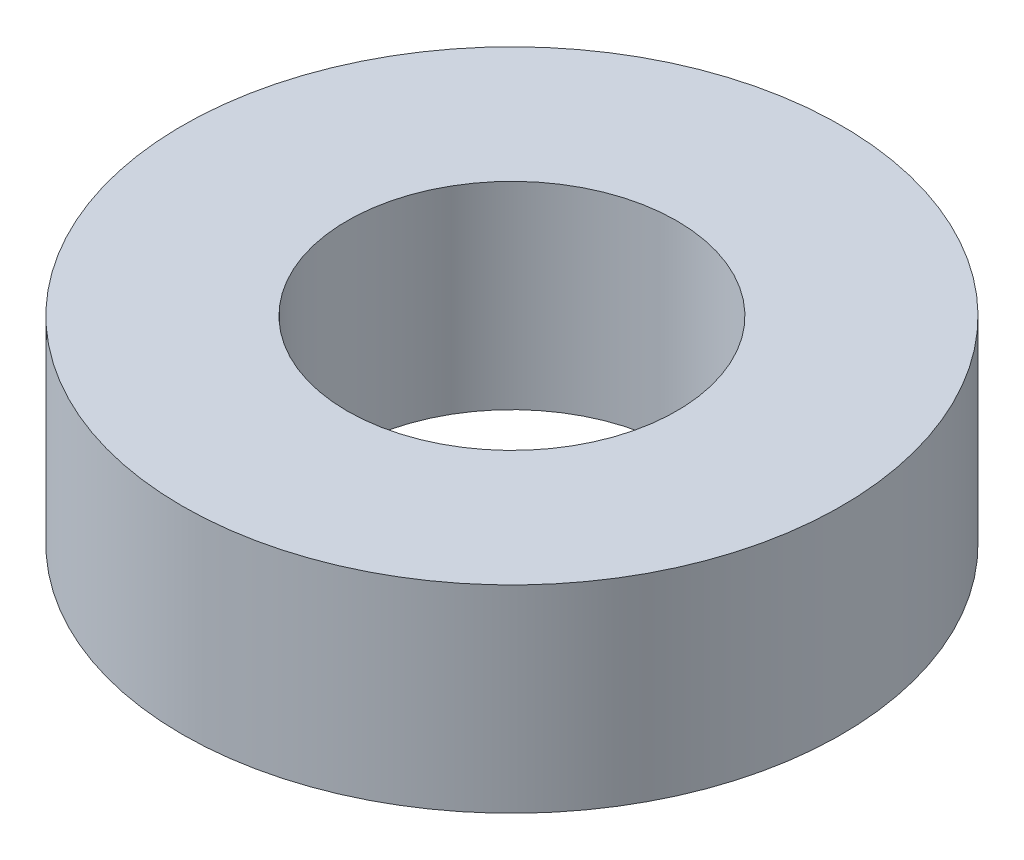
SolidWorks part; units mm, degrees
ref_plane "Front Plane" through (0, 0, 0) normal (0, 0, 1) x (1, 0, 0)
ref_plane "Top Plane" through (0, 0, 0) normal (0, 1, 0) x (1, 0, 0)
ref_plane "Right Plane" through (0, 0, 0) normal (1, 0, 0) x (0, 0, -1)
sketch "Sketch1" plane through (0, 0, 0) normal (0, 1, 0) x (1, 0, 0)
  circle A0 centre (0, 0) radius 6.35
  circle A1 centre (0, 0) radius 12.7
  dimension "D1" = 12.7
  dimension "D2" = 25.4
extrude "Boss-Extrude1" add sketch "Sketch1" along normal blind 7.62
